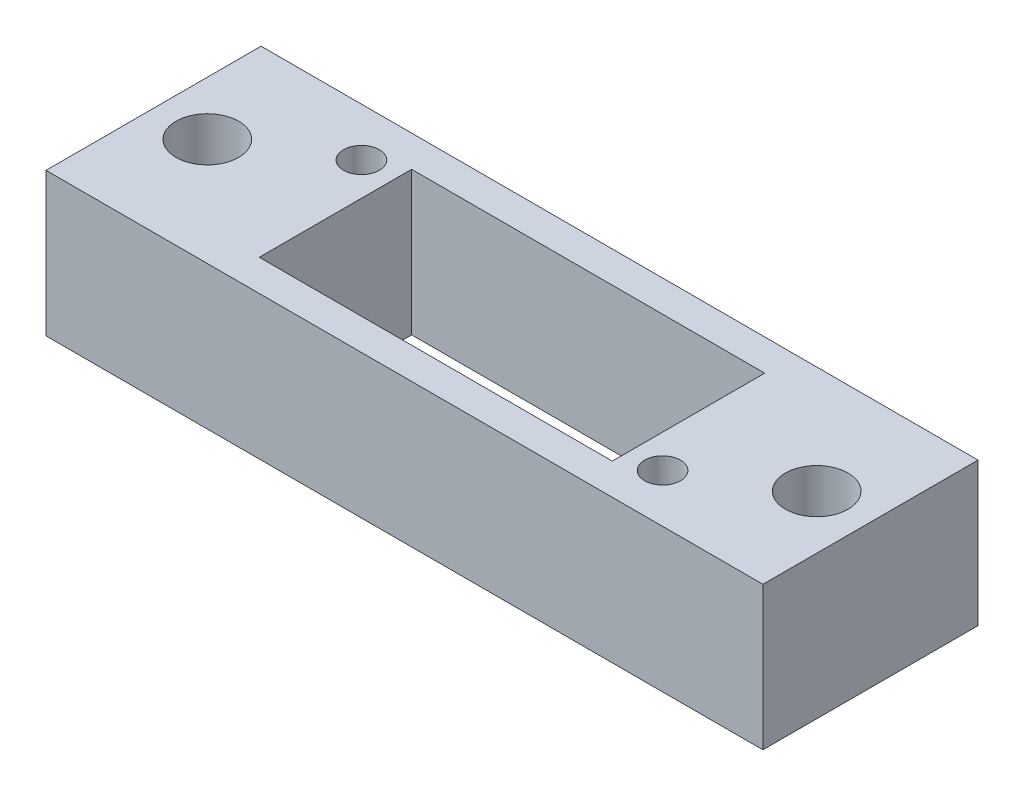
SolidWorks part; units mm, degrees
ref_plane "Front Plane" through (0, 0, 0) normal (0, 0, 1) x (1, 0, 0)
ref_plane "Top Plane" through (0, 0, 0) normal (0, 1, 0) x (1, 0, 0)
ref_plane "Right Plane" through (0, 0, 0) normal (1, 0, 0) x (0, 0, -1)
sketch "스케치1" plane through (0, 0, 0) normal (0, 1, 0) x (1, 0, 0)
  line L1 (-20, 6) -> (20, 6)
  line L2 (-20, 6) -> (-20, -6)
  line L3 (-20, -6) -> (20, -6)
  line L4 (20, 6) -> (20, -6)
  dimension "D1" = 20
  dimension "D2" = 40
  dimension "D3" = 12
  dimension "D4" = 6
extrude "보스-돌출1" add sketch "스케치1" along normal blind 8
sketch "스케치2" plane through (0, 8, 0) normal (0, 1, 0) x (1, 0, 0)
  line L1 (-9.85, 4.25) -> (9.85, 4.25)
  line L2 (-9.85, 4.25) -> (-9.85, -4.25)
  line L3 (-9.85, -4.25) -> (9.85, -4.25)
  line L4 (9.85, 4.25) -> (9.85, -4.25)
  dimension "D1" = 19.7
  dimension "D2" = 8.5
  dimension "D3" = 4.25
  dimension "D4" = 9.85
extrude "컷-돌출1" cut sketch "스케치2" against normal blind 8
sketch "스케치3" plane through (0, 8, 0) normal (0, 1, 0) x (1, 0, 0)
  line L0 (-16.0674, 3.3) -> (49983.9326, 3.3) construction
  line L1 (-16.4671, -3.3) -> (49983.5329, -3.3) construction
  line L2 (-11.7, 0.2598) -> (-11.7, -49999.7402) construction
  line L3 (11.7, 1.259) -> (11.7, -49998.741) construction
  line L6 (0, 0) -> (-50000, 0) construction
  circle A0 centre (-11.7, 3.3) radius 1
  circle A1 centre (11.7, -3.3) radius 1
  dimension "D1" = 3.3
  dimension "D2" = 3.3
  dimension "D3" = 11.7
  dimension "D4" = 11.7
extrude "컷-돌출2" cut sketch "스케치3" against normal blind 8
sketch "스케치4" plane through (0, 8, 0) normal (0, 1, 0) x (1, 0, 0)
  line L0 (0, 0) -> (50000, 0) construction
  line L1 (-17, 0) -> (-17, -50000) construction
  line L2 (17, 0) -> (17, -50000) construction
  circle A0 centre (-17, 0) radius 1.75
  circle A1 centre (17, 0) radius 1.75
  dimension "D1" = 17
  dimension "D2" = 17
extrude "컷-돌출3" cut sketch "스케치4" against normal blind 10
